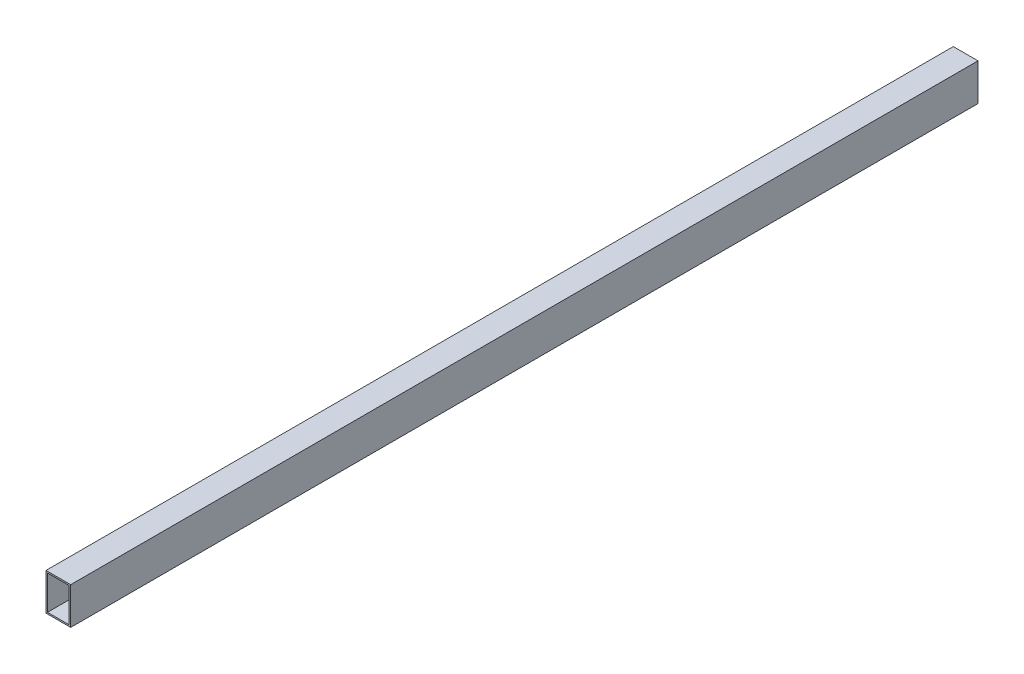
SolidWorks part; units mm, degrees
material "Plain Carbon Steel"
ref_plane "Front Plane" through (0, 0, 0) normal (0, 0, 1) x (1, 0, 0)
ref_plane "Top Plane" through (0, 0, 0) normal (0, 1, 0) x (1, 0, 0)
ref_plane "Right Plane" through (0, 0, 0) normal (1, 0, 0) x (0, 0, -1)
sketch "Sketch1" plane through (0, 0, 0) normal (0, 0, 1) x (1, 0, 0)
  line L0 (-50, 75) -> (50, -75) construction
  line L1 (-50, 75) -> (50, 75)
  line L2 (-50, 75) -> (-50, -75)
  line L3 (-50, -75) -> (50, -75)
  line L4 (50, 75) -> (50, -75)
  line L5 (-44, 69) -> (44, 69)
  line L6 (-44, 69) -> (-44, -69)
  line L7 (-44, -69) -> (44, -69)
  line L8 (44, 69) -> (44, -69)
  line L9 (-50, -75) -> (50, 75) construction
  point P11 (0, 0)
  dimension "D1" = 100
  dimension "D2" = 150
  dimension "D3" = 6
  dimension "D4" = 6
  dimension "D5" = 6
  dimension "D6" = 6
extrude "Boss-Extrude2" add sketch "Sketch1" along normal blind 3675
